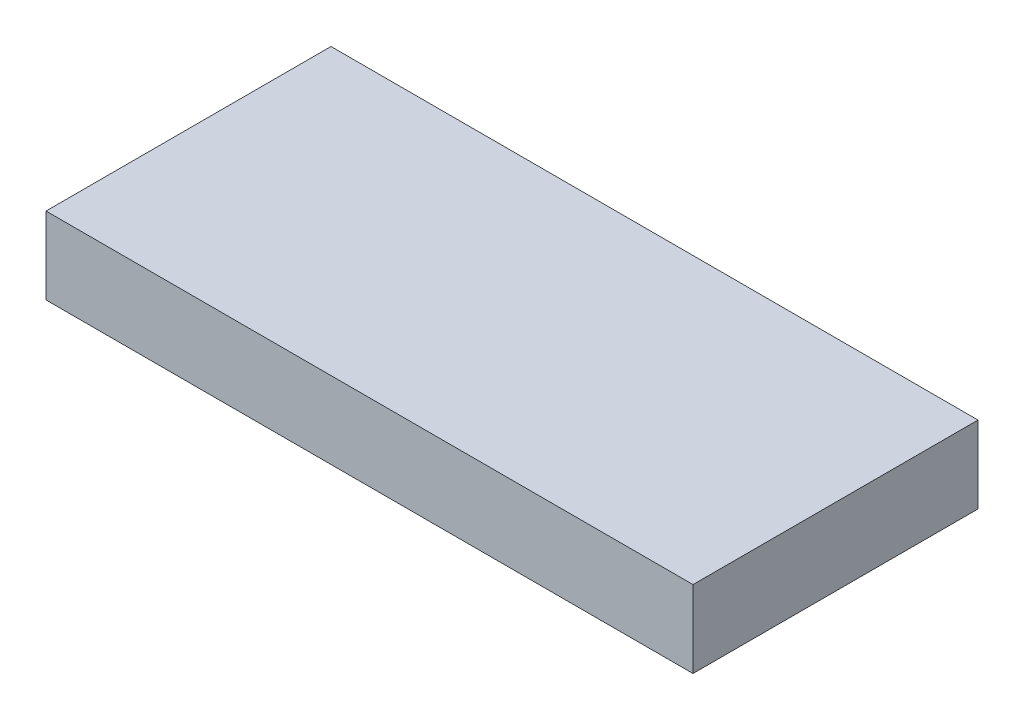
SolidWorks part; units mm, degrees
ref_plane "Спереди" through (0, 0, 0) normal (0, 0, 1) x (1, 0, 0)
ref_plane "Сверху" through (0, 0, 0) normal (0, 1, 0) x (1, 0, 0)
ref_plane "Справа" through (0, 0, 0) normal (1, 0, 0) x (0, 0, -1)
sketch "Эскиз1" plane through (0, 0, 0) normal (0, 1, 0) x (1, 0, 0)
  line L1 (0, 0) -> (42, 0)
  line L2 (0, 0) -> (0, 18.5)
  line L3 (0, 18.5) -> (42, 18.5)
  line L4 (42, 0) -> (42, 18.5)
  dimension "D1" = 18.5
  dimension "D2" = 42
extrude "Бобышка-Вытянуть1" add sketch "Эскиз1" along normal blind 5
